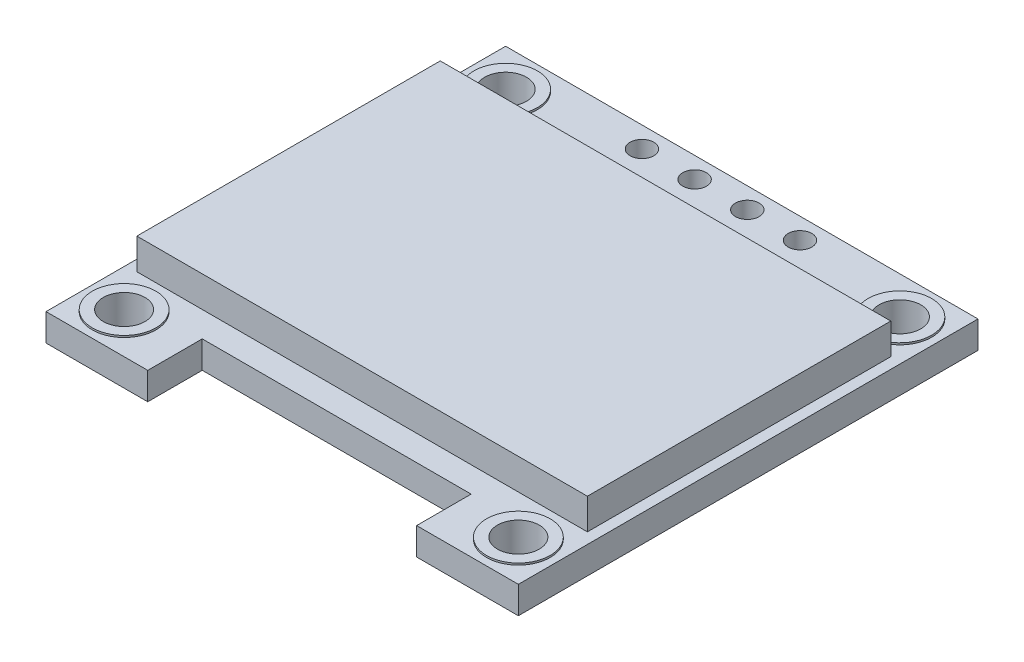
SolidWorks part; units mm, degrees
ref_plane "Front Plane" through (0, 0, 0) normal (0, 0, 1) x (1, 0, 0)
ref_plane "Top Plane" through (0, 0, 0) normal (0, 1, 0) x (1, 0, 0)
ref_plane "Right Plane" through (0, 0, 0) normal (1, 0, 0) x (0, 0, -1)
sketch "Sketch1" plane through (0, 0, 0) normal (0, 1, 0) x (1, 0, 0)
  line L1 (-10.6053, 7.3895) -> (15.3947, 7.3895)
  line L2 (-10.6053, 7.3895) -> (-10.6053, -17.9105)
  line L3 (-10.6053, -17.9105) -> (15.3947, -17.9105)
  line L4 (15.3947, 7.3895) -> (15.3947, -17.9105)
  dimension "D1" = 26
  dimension "D2" = 25.3
extrude "Boss-Extrude1" add sketch "Sketch1" along normal blind 1.5
sketch "Sketch2" plane through (0, 1.5, 0) normal (0, 1, 0) x (1, 0, 0)
  line L1 (-10.6053, -17.9105) -> (15.3947, -17.9105) construction
  line L2 (-5.0053, -17.9105) -> (9.7947, -17.9105)
  line L3 (-5.0053, -17.9105) -> (-5.0053, -14.9105)
  line L4 (-5.0053, -14.9105) -> (9.7947, -14.9105)
  line L5 (9.7947, -17.9105) -> (9.7947, -14.9105)
  point P0 (2.3947, -17.9105)
  point P1 (2.3947, -17.9105)
  dimension "D1" = 14.8
  dimension "D2" = 0
  dimension "D3" = 3
extrude "Cut-Extrude1" cut sketch "Sketch2" against normal blind 1.5
sketch "Sketch3" plane through (0, 1.5, 0) normal (0, 1, 0) x (1, 0, 0)
  line L0 (-10.6053, 7.3895) -> (-10.6053, -17.9105) construction
  line L1 (-10.6053, -17.9105) -> (-5.0053, -17.9105) construction
  line L2 (9.7947, -17.9105) -> (15.3947, -17.9105) construction
  line L3 (15.3947, -17.9105) -> (15.3947, 7.3895) construction
  line L4 (15.3947, 7.3895) -> (-10.6053, 7.3895) construction
  circle A0 centre (-8.4553, 5.2395) radius 1.15
  circle A1 centre (13.2447, 5.2395) radius 1.15
  circle A2 centre (13.2447, -15.7605) radius 1.15
  circle A3 centre (-8.4553, -15.7605) radius 1.15
  dimension "D1" = 2.3
  dimension "D2" = 2.3
  dimension "D3" = 2.3
  dimension "D4" = 2.3
  dimension "D5" = 2.15
  dimension "D6" = 2.15
  dimension "D7" = 2.15
  dimension "D8" = 2.15
  dimension "D9" = 2.15
  dimension "D10" = 2.15
  dimension "D11" = 2.15
  dimension "D12" = 2.15
extrude "Cut-Extrude2" cut sketch "Sketch3" against normal blind 1.5
sketch "Sketch4" plane through (0, 1.5, 0) normal (0, 1, 0) x (1, 0, 0)
  circle A0 centre (-8.4553, 5.2395) radius 1.15
  circle A1 centre (-8.4553, 5.2395) radius 1.75
  circle A2 centre (13.2447, 5.2395) radius 1.15
  circle A3 centre (13.2447, 5.2395) radius 1.75
  circle A4 centre (13.2447, -15.7605) radius 1.15
  circle A5 centre (13.2447, -15.7605) radius 1.75
  circle A6 centre (-8.4553, -15.7605) radius 1.15
  circle A7 centre (-8.4553, -15.7605) radius 1.75
  dimension "D1" = 0.6
  dimension "D2" = 0.6
  dimension "D3" = 0.6
  dimension "D4" = 0.6
extrude "Boss-Extrude3" add sketch "Sketch4" along normal blind 0.1 and the other way offset from surface (1.6 mm away) 0.1 contours A0
sketch "Sketch6" plane through (0, 1.5, 0) normal (0, 1, 0) x (1, 0, 0)
  line L0 (15.3947, 7.3895) -> (-10.6053, 7.3895) construction
  line L1 (-10.0053, 3.1895) -> (14.7947, 3.1895)
  line L2 (-10.0053, 3.1895) -> (-10.0053, -13.5105)
  line L3 (-10.0053, -13.5105) -> (14.7947, -13.5105)
  line L4 (14.7947, 3.1895) -> (14.7947, -13.5105)
  line L5 (9.7947, -17.9105) -> (15.3947, -17.9105) construction
  point P4 (2.3947, 3.1895)
  point P7 (2.3947, 7.3895)
  dimension "D1" = 24.8
  dimension "D2" = 16.7
  dimension "D3" = 0
  dimension "D4" = 21.1
extrude "Boss-Extrude4" add sketch "Sketch6" along normal blind 1.7
sketch "Sketch7" plane through (0, 0, 0) normal (0, -1, 0) x (1, 0, 0)
  line L1 (-8.1553, 5.6105) -> (12.9447, 5.6105)
  line L2 (-8.1553, 5.6105) -> (-8.1553, 2.3105)
  line L3 (-8.1553, 2.3105) -> (12.9447, 2.3105)
  line L4 (12.9447, 5.6105) -> (12.9447, 2.3105)
  line L5 (-3.3053, -0.3895) -> (9.5947, -0.3895)
  line L6 (-3.3053, -0.3895) -> (-3.3053, -3.6895)
  line L7 (-3.3053, -3.6895) -> (9.5947, -3.6895)
  line L8 (9.5947, -0.3895) -> (9.5947, -3.6895)
  line L10 (9.7947, 14.9105) -> (-5.0053, 14.9105) construction
  line L11 (9.7947, 17.9105) -> (15.3947, 17.9105) construction
  line L12 (-10.6053, -7.3895) -> (-10.6053, 17.9105) construction
  line L13 (15.3947, -7.3895) -> (-10.6053, -7.3895) construction
  point P10 (2.3947, 14.9105)
  point P11 (2.3947, 5.6105)
  dimension "D1" = 21.1
  dimension "D2" = 3.3
  dimension "D3" = 0
  dimension "D4" = 15.6
  dimension "D5" = 12.9
  dimension "D6" = 3.3
  dimension "D7" = 20.2
  dimension "D8" = 7
extrude "Boss-Extrude5" add sketch "Sketch7" along normal blind 0.8
sketch "Sketch8" plane through (0, 0, 0) normal (0, -1, 0) x (1, 0, 0)
  line L0 (-10.6053, -7.3895) -> (-10.6053, 17.9105) construction
  line L1 (15.3947, 17.9105) -> (15.3947, -7.3895) construction
  circle A0 centre (-1.9553, -6.2411) radius 0.65
  circle A1 centre (0.9447, -6.2411) radius 0.65
  circle A2 centre (3.8447, -6.2411) radius 0.65
  circle A3 centre (6.7447, -6.2411) radius 0.65
  dimension "D1" = 1.3
  dimension "D3" = 8.65
  dimension "D4" = 8.65
  dimension "D2" = 4
extrude "Cut-Extrude4" cut sketch "Sketch8" against normal through all contours A1
